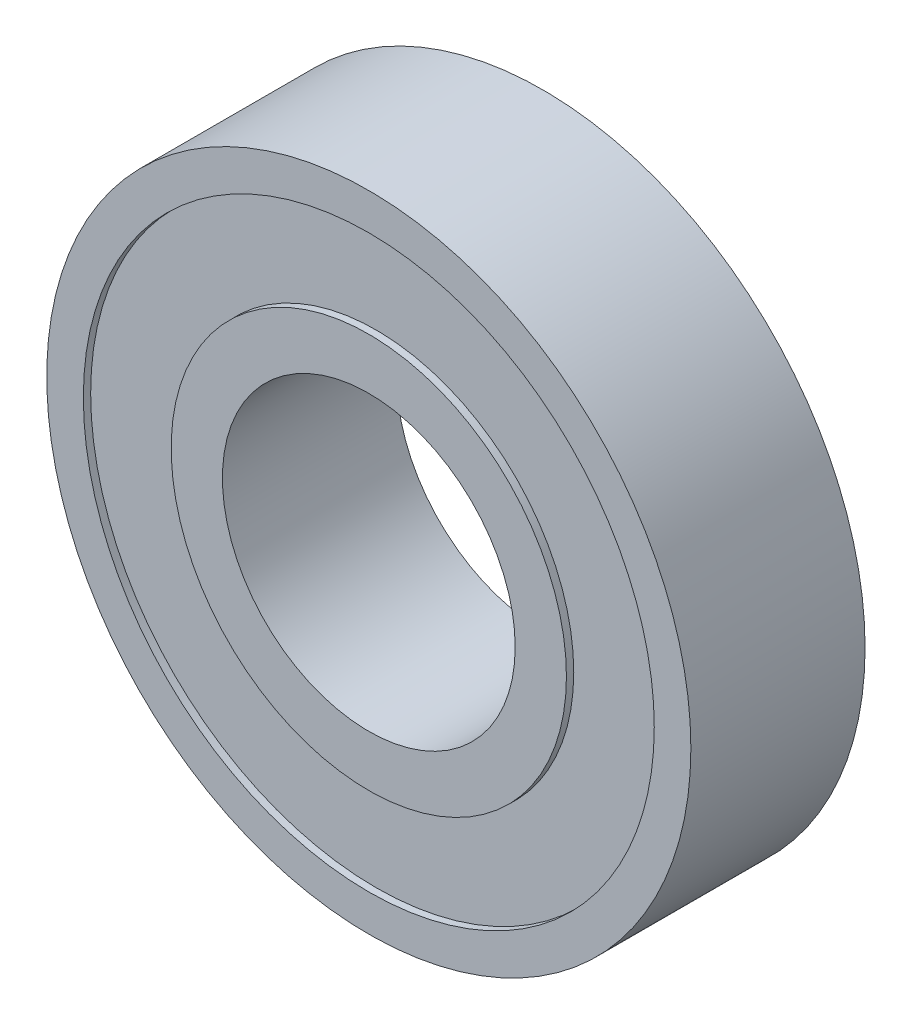
SolidWorks part; units mm, degrees
ref_plane "Front Plane" through (0, 0, 0) normal (0, 0, 1) x (1, 0, 0)
ref_plane "Top Plane" through (0, 0, 0) normal (0, 1, 0) x (1, 0, 0)
ref_plane "Right Plane" through (0, 0, 0) normal (1, 0, 0) x (0, 0, -1)
sketch "Sketch3" plane through (0, 0, 0) normal (0, 0, 1) x (1, 0, 0)
  circle A0 centre (0, 0) radius 11
  circle A1 centre (0, 0) radius 5
  dimension "D1" = 22
  dimension "D2" = 10
extrude "Boss-Extrude1" add sketch "Sketch3" along normal blind 5.95
sketch "Sketch4" plane through (0, 0, 5.95) normal (0, 0, 1) x (1, 0, 0)
  circle A0 centre (0, 0) radius 6.75
  circle A1 centre (0, 0) radius 9.75
  dimension "D1" = 19.5
  dimension "D2" = 13.5
extrude "Cut-Extrude1" cut sketch "Sketch4" against normal blind 0.25 contours A0
ref_plane "Plane1" through (0, 0, 2.975) normal (0, 0, 1) x (1, 0, 0)
mirror "Mirror1" about plane through (0, 0, 2.975) normal (0, 0, 1) of "Cut-Extrude1"
